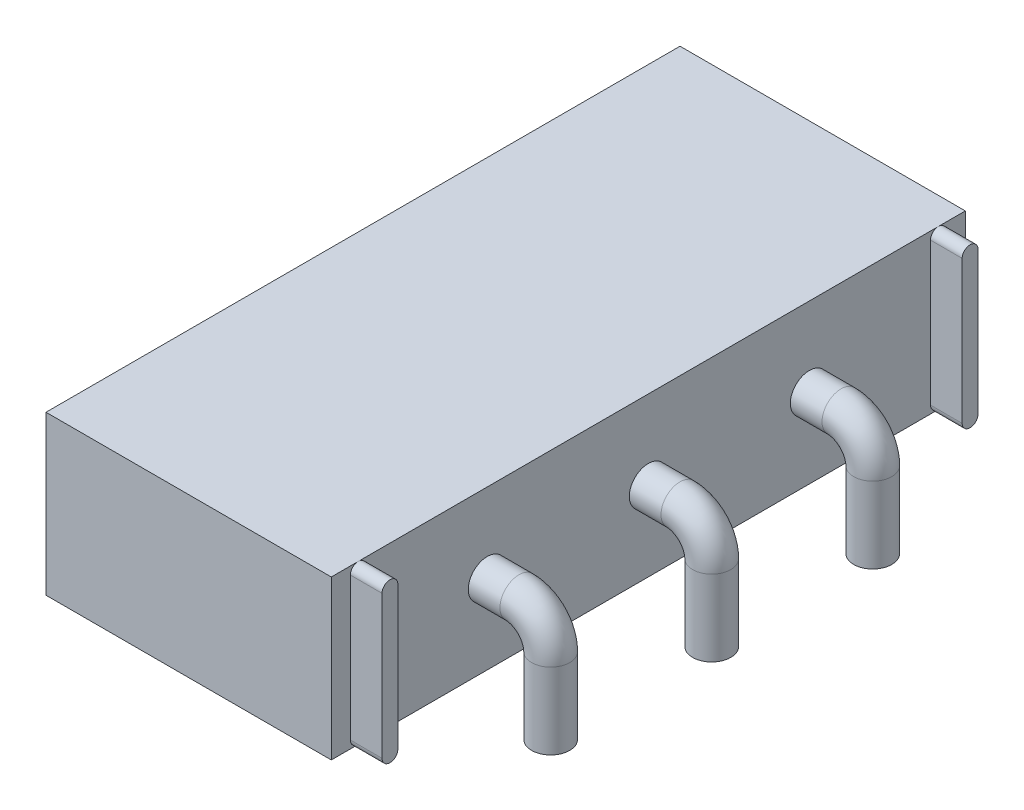
SolidWorks part; units mm, degrees
ref_plane "Front Plane" through (0, 0, 0) normal (0, 0, 1) x (1, 0, 0)
ref_plane "Top Plane" through (0, 0, 0) normal (0, 1, 0) x (1, 0, 0)
ref_plane "Right Plane" through (0, 0, 0) normal (1, 0, 0) x (0, 0, -1)
sketch "Sketch1" plane through (0, 0, 0) normal (0, 1, 0) x (1, 0, 0)
  line L1 (0, 0) -> (4.5, 0)
  line L2 (0, 0) -> (0, 10)
  line L3 (0, 10) -> (4.5, 10)
  line L4 (4.5, 0) -> (4.5, 10)
  dimension "D1" = 10
  dimension "D2" = 4.5
extrude "Body Shape" add sketch "Sketch1" along normal blind 2.5 contours L4 L3 L2 L1
sketch "Sketch2" plane through (0, 0, 0) normal (-1, 0, 0) x (0, 0, 1)
  line L0 (-10, 1.25) -> (0, 1.25) construction
  line L1 (-10, 2.5) -> (-10, 0) construction
  line L2 (0, 2.5) -> (0, 0) construction
  line L3 (-5, 0) -> (-5, 2.5) construction
  line L4 (0, 0) -> (-10, 0) construction
  line L5 (0, 2.5) -> (-10, 2.5) construction
  circle A0 centre (-9.35, 1.25) radius 0.5
  dimension "D1" = 1
  dimension "D2" = 0.65
extrude "Off Hole" cut sketch "Sketch2" against normal blind 1
sketch "Sketch3" plane through (0, 0, 0) normal (-1, 0, 0) x (0, 0, 1)
  line L0 (-10, 1.25) -> (0, 1.25) construction
  line L1 (-5, 0) -> (-5, 2.5) construction
  line L2 (-10, 1.25) -> (0, 1.25) construction
  line L3 (-5, 0) -> (-5, 2.5) construction
  circle A0 centre (-0.65, 1.25) radius 0.5
  circle A1 centre (-9.35, 1.25) radius 0.5 construction
  circle A2 centre (-9.35, 1.25) radius 0.5 construction
extrude "On hole" cut sketch "Sketch3" against normal blind 0.1
sketch "Sketch4" plane through (4.5, 0, 0) normal (1, 0, 0) x (0, 0, -1)
  line L0 (5, 0) -> (5, 2.5) construction
  line L1 (10, 1.25) -> (0, 1.25) construction
  line L2 (5, 0) -> (5, 2.5) construction
  line L3 (10, 1.25) -> (0, 1.25) construction
  circle A0 centre (7.54, 1.25) radius 0.3
  circle A1 centre (5, 1.25) radius 0.3
  circle A2 centre (2.46, 1.25) radius 0.3
  dimension "D1" = 0.6
  dimension "D2" = 2.54
  dimension "D3" = 3
sketch "Sketch8" plane through (4.5, 0, 0) normal (1, 0, 0) x (0, 0, -1)
  line L0 (0, 2.5) -> (0, 0) construction
  line L1 (0, 0) -> (10, 0) construction
  line L2 (0, 2.5) -> (10, 2.5) construction
  line L3 (5, 2.5) -> (5, 0) construction
  line L4 (9.7, 0.1232) -> (9.7, 2.3768)
  line L5 (9.45, 2.3768) -> (9.45, 0.1232)
  line L14 (0.3, 0.1232) -> (0.3, 2.3768)
  line L15 (0.55, 2.3768) -> (0.55, 0.1232)
  arc A0 (0.3, 2.3768) -> (0.55, 2.3768) centre (0.425, 2.375) cw
  arc A1 (0.55, 0.1232) -> (0.3, 0.1232) centre (0.425, 0.125) cw
  arc A2 (9.45, 0.1232) -> (9.7, 0.1232) centre (9.575, 0.125) ccw
  arc A3 (9.7, 2.3768) -> (9.45, 2.3768) centre (9.575, 2.375) ccw
  dimension "D1" = 0.125
  dimension "D2" = 0.3
  dimension "D3" = 0.25
ref_plane "Plane2" through (0, 0, -7.54) normal (0, 0, 1) x (1, 0, 0)
sketch "Sketch9" plane through (0, 0, -7.54) normal (0, 0, 1) x (1, 0, 0)
  line L0 (4.5, 1.25) -> (5, 1.25)
  line L1 (4.5, 0.95) -> (4.5, 1.55) construction
  line L2 (5.5, 0.75) -> (5.5, -0.45)
  line L4 (4.5, 2.5) -> (4.5, 0) construction
  arc A0 (5, 1.25) -> (5.5, 0.75) centre (5, 0.75) cw
  dimension "D1" = 1
  dimension "D2" = 0.5
  dimension "D3" = 1.7
extrude "bottom flaps" add sketch "Sketch8" along normal blind 0.5
sweep "pins" add profiles "Sketch4" path "Sketch9"
